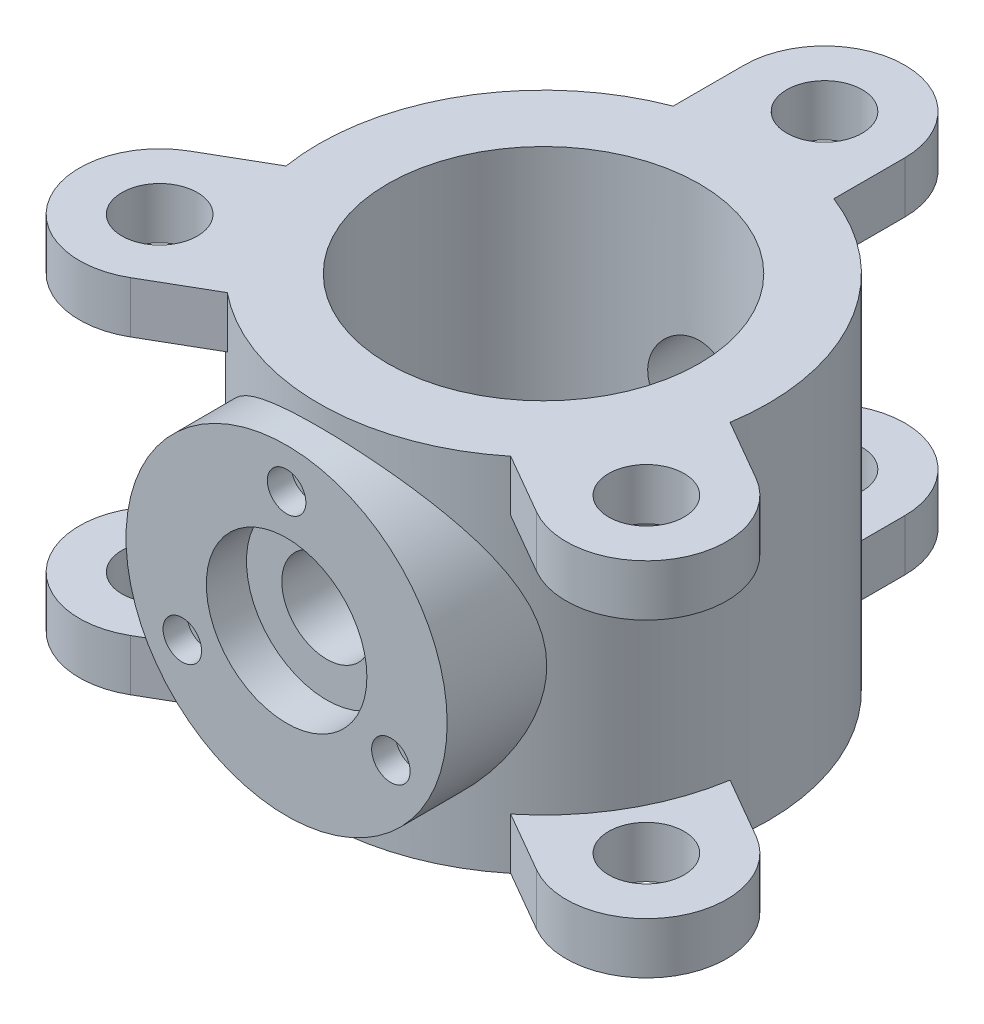
SolidWorks part; units mm, degrees
ref_plane "Front Plane" through (0, 0, 0) normal (0, 0, 1) x (1, 0, 0)
ref_plane "Top Plane" through (0, 0, 0) normal (0, 1, 0) x (1, 0, 0)
ref_plane "Right Plane" through (0, 0, 0) normal (1, 0, 0) x (0, 0, -1)
sketch "Sketch2" plane through (0, 0, 0) normal (0, 1, 0) x (1, 0, 0)
  circle A0 centre (0, 0) radius 97
  circle A1 centre (0, 0) radius 140
  dimension "D1" = 280
  dimension "D2" = 194
extrude "Boss-Extrude1" add sketch "Sketch2" along normal blind 225
sketch "Sketch3" plane through (0, 225, 0) normal (0, 1, 0) x (1, 0, 0)
  line L1 (-50, 105) -> (50, 105)
  line L2 (-50, 105) -> (-50, 175)
  line L3 (-50, 175) -> (50, 175) construction
  line L4 (50, 105) -> (50, 175)
  line L5 (-50, 105) -> (50, 175) construction
  line L6 (-50, 175) -> (50, 105) construction
  circle A0 centre (0, 0) radius 140 construction
  arc A2 (50, 175) -> (-50, 175) centre (0, 175) ccw
  circle A3 centre (0, 175) radius 23.5
  point P0 (0, 140)
  dimension "D2" = 50
  dimension "D3" = 47
  dimension "D1" = 175
extrude "Boss-Extrude2" add sketch "Sketch3" against normal blind 32
pattern_circular "CirPattern1" count 3 over 360 about axis through (0, 0, 0) along (0, 1, 0) of "Boss-Extrude2"
ref_plane "Plane1" through (0, 112.5, 0) normal (0, 1, 0) x (1, 0, 0)
mirror "Mirror1" about plane through (0, 112.5, 0) normal (0, 1, 0) of "CirPattern1", "Boss-Extrude2"
ref_plane "Plane2" through (0, 0, 160) normal (0, 0, 1) x (1, 0, 0)
sketch "Sketch4" plane through (0, 0, 160) normal (0, 0, 1) x (1, 0, 0)
  line L0 (-88.2475, 0) -> (88.2475, 0) construction
  circle A0 centre (0, 112.5) radius 100
  dimension "D1" = 200
  dimension "D2" = 112.5
extrude "Boss-Extrude3" add sketch "Sketch4" against normal up to next contours A0
sketch "Sketch6" plane through (0, 0, 160) normal (0, 0, 1) x (1, 0, 0)
  circle A0 centre (0, 112.5) radius 50
  dimension "D1" = 100
extrude "Cut-Extrude1" cut sketch "Sketch6" against normal blind 25
sketch "Sketch7" plane through (0, 0, 135) normal (0, 0, 1) x (1, 0, 0)
  circle A0 centre (0, 112.5) radius 28
  dimension "D1" = 56
extrude "Cut-Extrude2" cut sketch "Sketch7" against normal through all
sketch "Sketch8" plane through (0, 0, 160) normal (0, 0, 1) x (1, 0, 0)
  circle A0 centre (0, 187.5) radius 12
  circle A1 centre (0, 112.5) radius 28 construction
  point P4 (0, 0)
  point P7 (0, 0)
  point P10 (0, 0)
  point P11 (0, 0)
  dimension "D1" = 24
  dimension "D2" = 75
extrude "Cut-Extrude3" cut sketch "Sketch8" against normal blind 15
pattern_circular "CirPattern2" count 3 over 360 about axis through (0, 112.5, 0) along (0, 0, 1) of "Cut-Extrude3"
